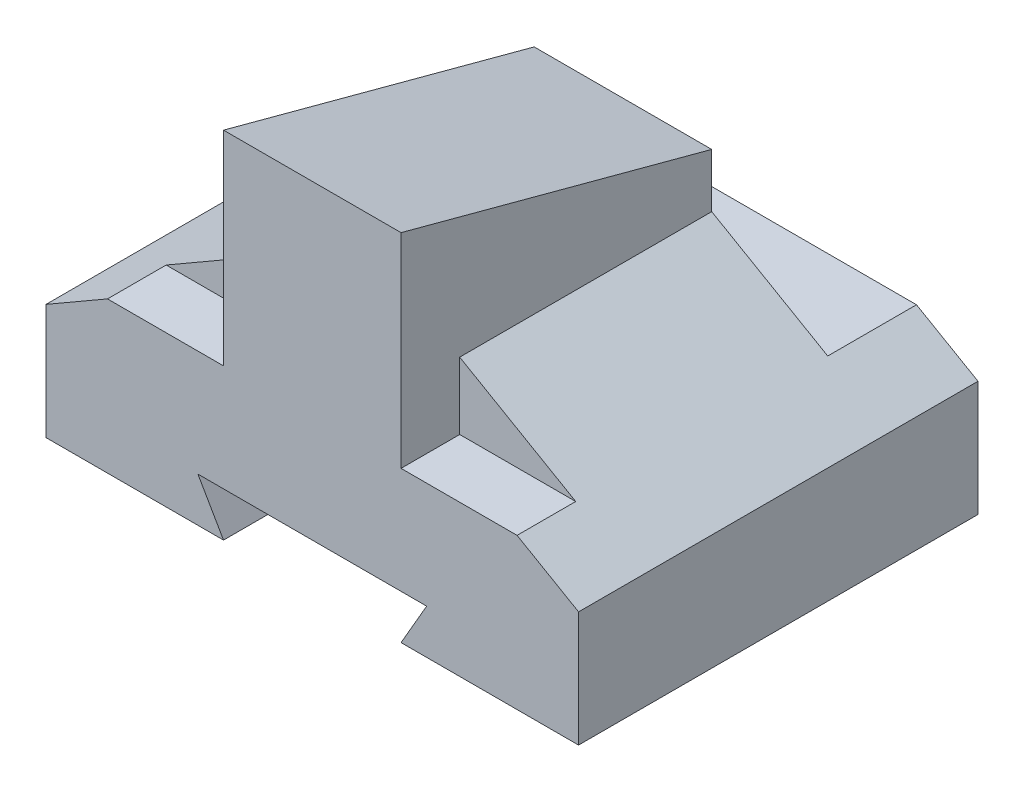
SolidWorks part; units mm, degrees
material "Copper"
ref_plane "Front Plane" through (0, 0, 0) normal (0, 0, 1) x (1, 0, 0)
ref_plane "Top Plane" through (0, 0, 0) normal (0, 1, 0) x (1, 0, 0)
ref_plane "Right Plane" through (0, 0, 0) normal (1, 0, 0) x (0, 0, -1)
sketch "Sketch2" plane through (0, 0, 0) normal (0, 1, 0) x (1, 0, 0)
  line L1 (30, 22.5) -> (-30, 22.5)
  line L2 (30, 22.5) -> (30, -22.5)
  line L3 (30, -22.5) -> (-30, -22.5)
  line L4 (-30, 22.5) -> (-30, -22.5)
  line L5 (30, 22.5) -> (-30, -22.5) construction
  line L6 (30, -22.5) -> (-30, 22.5) construction
  point P0 (0, 0)
  dimension "D1" = 45
  dimension "D2" = 60
extrude "Boss-Extrude1" add sketch "Sketch2" along normal blind 13
sketch "Sketch3" plane through (0, 0, 22.5) normal (0, 0, 1) x (1, 0, 0)
  line L0 (-30, 0) -> (30, 0) construction
  line L1 (30, 13) -> (30, 0) construction
  line L2 (-30, 13) -> (30, 13) construction
  line L3 (-30, 13) -> (-30, 0) construction
  line L4 (-30, 0) -> (30, 0)
  line L5 (30, 13) -> (30, 0)
  line L6 (-30, 13) -> (30, 13)
  line L7 (-30, 13) -> (-30, 0)
  line L8 (-30, 13) -> (0, 30.3205)
  line L9 (0, 30.3205) -> (30, 13)
  line M7 (30, 13) -> (-30, 13)
  dimension "D1" = 60
  dimension "D2" = 60
extrude "Boss-Extrude2" add sketch "Sketch3" against normal blind 45 contours L9 L8 M7
ref_plane "Plane2" through (0, 38, 0) normal (0, -1, 0) x (-1, 0, 0)
sketch "Sketch11" plane through (0, 38, 0) normal (0, -1, 0) x (-1, 0, 0)
  line L0 (-30, 12.5) -> (30, 12.5)
  line L1 (-30, -15.8919) -> (30, -15.8919)
  line L2 (30, 12.5) -> (30, 22.5)
  line L3 (-30, -15.8919) -> (-30, -22.5)
  line L4 (30, -22.5) -> (30, 22.5)
  line L5 (30, 22.5) -> (-30, 22.5)
  line L6 (-30, 22.5) -> (-30, -22.5)
  line L7 (-30, -22.5) -> (30, -22.5)
  line L8 (30, -22.5) -> (30, -15.8919)
  line L9 (30, 22.5) -> (-30, 22.5)
  line L10 (-30, 22.5) -> (-30, 12.5)
  line L11 (-30, -22.5) -> (30, -22.5)
  dimension "D2" = 10
  dimension "D3" = 6.6081
  dimension "D1" = 0
extrude "Cut-Extrude2" cut sketch "Sketch11" along normal blind 21
ref_plane "Plane3" through (0, 40, 0) normal (0, -1, 0) x (-1, 0, 0)
sketch "Sketch12" plane through (0, 40, 0) normal (0, -1, 0) x (-1, 0, 0)
  line L0 (-10, -22.5) -> (-10, 12.5)
  line L1 (-23.0718, -22.5) -> (23.0718, -22.5) construction
  line L2 (0, 12.5) -> (-23.0718, 12.5) construction
  line L3 (-10, 12.5) -> (10, 12.5)
  line L4 (-23.0718, 12.5) -> (23.0718, 12.5) construction
  line L5 (10, 12.5) -> (10, -22.5)
  line L6 (10, -22.5) -> (-10, -22.5)
  point P6 (0, -22.5)
  dimension "D1" = 20
extrude "Boss-Extrude3" add sketch "Sketch12" along normal up to next
draft "Draft1" type of draft neutral plane draft angle 15 faces to draft 1 face at (0, 40, 5) neutral plane through (30, 13, 22.5) neutral plane normal (0, 0, 1) reverse direction yes parameters "D1"=15
sketch "Sketch16" plane through (0, 0, -22.5) normal (0, 0, -1) x (-1, 0, 0)
  line L0 (-10, 0) -> (-12.8868, 5)
  line L1 (-12.8868, 5) -> (12.8868, 5)
  line L2 (12.8868, 5) -> (10, 0)
  line L3 (10, 0) -> (-10, 0)
  line L6 (30, 13) -> (23.0718, 17)
  line L7 (23.0718, 17) -> (-23.0718, 17)
  line L8 (-23.0718, 17) -> (-30, 13)
  line L9 (-30, 13) -> (-30, 0)
  line L10 (-30, 0) -> (30, 0)
  line L11 (30, 0) -> (30, 13)
  line L12 (30, 13) -> (23.0718, 17)
  line L13 (23.0718, 17) -> (-23.0718, 17)
  line L14 (-23.0718, 17) -> (-30, 13)
  line L15 (-30, 13) -> (-30, 0)
  line L16 (-30, 0) -> (30, 0)
  line L17 (30, 0) -> (30, 13)
  point P8 (0, 0)
  line M15 (-30, 0) -> (30, 0)
  dimension "D2" = 20
  dimension "D3" = 5
  dimension "D1" = 0
extrude "Cut-Extrude3" cut sketch "Sketch16" against normal through all contours L2 L1 L0 M15
sketch "Sketch17" plane through (0, 0, -22.5) normal (0, 0, -1) x (-1, 0, 0)
